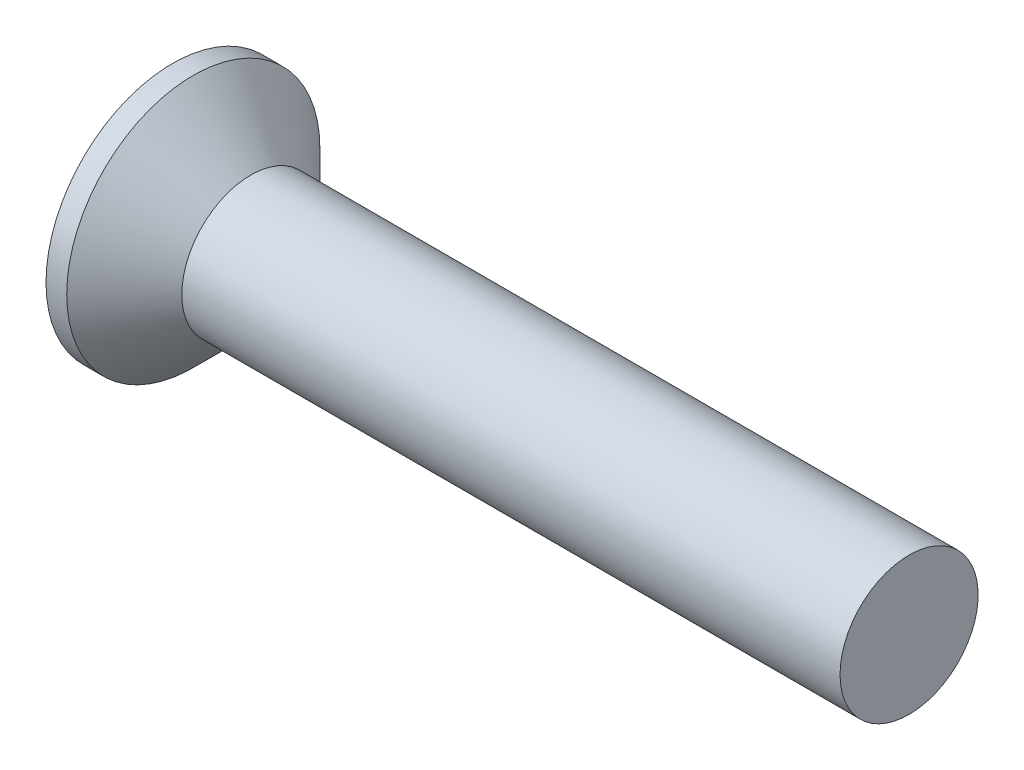
SolidWorks part; units mm, degrees
revolve "Base-Revolve" add sketch "BodySke" angle 360 about L5
sketch "BodySke" plane through (0, 0, 0) normal (0, 0, 1) x (1, 0, 0)
  line L0 (0, 0) -> (0, 2.75)
  line L1 (0, 2.75) -> (0.45, 2.75)
  line L2 (1.7, 1.5) -> (16, 1.5)
  line L3 (16, 1.5) -> (16, 0)
  line L4 (16, 0) -> (0, 0)
  line L5 (-6.35, 0) -> (82.55, 0) construction
  line L6 (1.7, -1.5) -> (16, -1.5) construction
  line L7 (0.45, -2.75) -> (1.7, -1.5) construction
  line L8 (0.45, 2.75) -> (1.7, 1.5)
  line L9 (0, -2.75) -> (0.45, -2.75) construction
  line L10 (2.2, 3.0875) -> (2.2, -6.4375) construction
  line L11 (0, 6.35) -> (0, -3.175) construction
  dimension "Diameter" = 3
  dimension "Length" = 16
  dimension "Head_ht" = 1.7
  dimension "Head_dia" = 5.5
  dimension "Head_ang" = 90
  dimension "D6" = 0.45
  dimension "Advance" = 0.5
  dimension "Thread_nom" = 16
cosmetic thread "ThreadCosmetic" parameters "Thread_length"=13.8, "Thread_minor"=2.439
extrude "Slot" [suppressed] cut sketch "Sketch2" against normal blind 0.9
sketch "Sketch2" plane through (0, 0, 0) normal (-1, 0, 0) x (0, 0, 1)
  line L0 (-2.75, -0.5) -> (2.75, -0.5)
  line L1 (-2.75, -0.5) -> (-2.75, 0.5)
  line L2 (2.75, 0.5) -> (-2.75, 0.5)
  line L3 (2.75, 0.5) -> (2.75, -0.5)
  dimension "Slot_width" = 1
  dimension "D1" = 0.5
  dimension "D2" = 5.5
  dimension "D3" = 2.75
ref_plane "Plane1" through (0, 0, 0) normal (0, 0, 1) x (1, 0, 0)
ref_plane "Plane2" through (0, 0, 0) normal (0, 1, 0) x (1, 0, 0)
ref_plane "Plane3" through (0, 0, 0) normal (1, 0, 0) x (0, 0, -1)
sketch "Sketch3" plane through (0, 0, 0) normal (-1, 0, 0) x (0, 0, 1)
  line L0 (-0.395, 1.55) -> (0.395, 1.55)
  line L1 (0.395, 1.55) -> (0.395, -1.55)
  line L2 (0.395, -1.55) -> (-0.395, -1.55)
  line L3 (-0.395, -1.55) -> (-0.395, 1.55)
  dimension "Cross_dia" = 3.1
  dimension "Cross_width" = 0.79
  dimension "D1" = 1.55
  dimension "D2" = 0.395
ref_plane "Plane4" through (2.08, 0, 0) normal (-1, 0, 0) x (0, 0, 1)
sketch "Sketch4" plane through (2.08, 0, 0) normal (-1, 0, 0) x (0, 0, 1)
  line L0 (-0.1975, 0.1975) -> (0.1975, 0.1975)
  line L3 (0.1975, 0.1975) -> (0.1975, -0.1975)
  line L4 (0.1975, -0.1975) -> (-0.1975, -0.1975)
  line L5 (-0.1975, -0.1975) -> (-0.1975, 0.1975)
  dimension "D2" = 0.395
  dimension "D1" = 0.395
  dimension "D3" = 0.1975
  dimension "D4" = 0.1975
loft "Cross" cut profiles "Sketch3", "Sketch4"
pattern_circular "CirPattern1" count 2 every 90 about axis through (0, 0, 0) along (1, 0, 0) of "Cross"
sketch "ThdSchSke" plane through (0, 0, 0) normal (0, 0, 1) x (1, 0, 0)
  line L0 (2.2, -1.2195) -> (2.0036, -1.5)
  line L1 (2.2, -1.2195) -> (2.3964, -1.5)
  line L2 (2.3964, -1.5) -> (2.3964, -1.875)
  line L3 (-3.175, 0) -> (5.1513, 0) construction
  line L5 (2.3964, -1.875) -> (2.0036, -1.875)
  line L6 (2.0036, -1.875) -> (2.0036, -1.5)
  line L7 (0, 2.75) -> (0, -2.75) construction
  dimension "Diameter" = 3
  dimension "Thread_minor" = 2.439
  dimension "Start" = 2.2
revolve "ThreadSchematic" [suppressed] cut sketch "ThdSchSke" angle 360 about L3
pattern_linear "ThdSchPat" [suppressed]
equation "\"D1@Sketch3\" = \"Cross_dia@Sketch3\" / 2"
equation "\"D2@Sketch3\" = \"Cross_width@Sketch3\" / 2"
equation "\"D1@Sketch4\" = \"Cross_width@Sketch3\" *.5"
equation "\"D2@Sketch4\" = \"D1@Sketch4\""
equation "\"D4@Sketch4\" = \"D2@Sketch4\" / 2"
equation "\"D3@Sketch4\" = \"D1@Sketch4\" / 2"
equation "\"D1@Sketch2\" = \"Slot_width@Sketch2\" / 2"
equation "\"D2@Sketch2\" = \"Head_dia@BodySke\""
equation "\"D3@Sketch2\" = \"D2@Sketch2\" / 2"
equation "\"Thread_length@ThreadCosmetic\" = ((sgn( (\"Length@BodySke\" - \"Advance@BodySke\" - \"Head_ht@BodySke\" ) - \"Thread_nom@BodySke\" )-1)*( (\"Length@BodySke\" - \"Advance@BodySke\" - \"Head_ht@BodySke\" ) - \"Thread_nom@BodySke\" ))/-2+ \"Thread_nom@BodySke\""
equation "\"Thread_minor@ThdSchSke\" = \"Thread_minor@ThreadCosmetic\""
equation "\"Diameter@ThdSchSke\" = \"Diameter@BodySke\""
equation "\"Overcut@ThdSchSke\" = \"Diameter@BodySke\" * 1.25"
equation "\"Start@ThdSchSke\" = 0.000001 + \"Length@BodySke\" - \"Thread_length@ThreadCosmetic\"  '---Countersunk---"
equation "\"Num_threads@ThdSchPat\" = int( \"Thread_length@ThreadCosmetic\" / \"Advance@BodySke\" + 0.999 )  + 1"
equation "\"Advance@ThdSchPat\" = \"Thread_length@ThreadCosmetic\" /  (\"Num_threads@ThdSchPat\" - 1) 'relax it"
